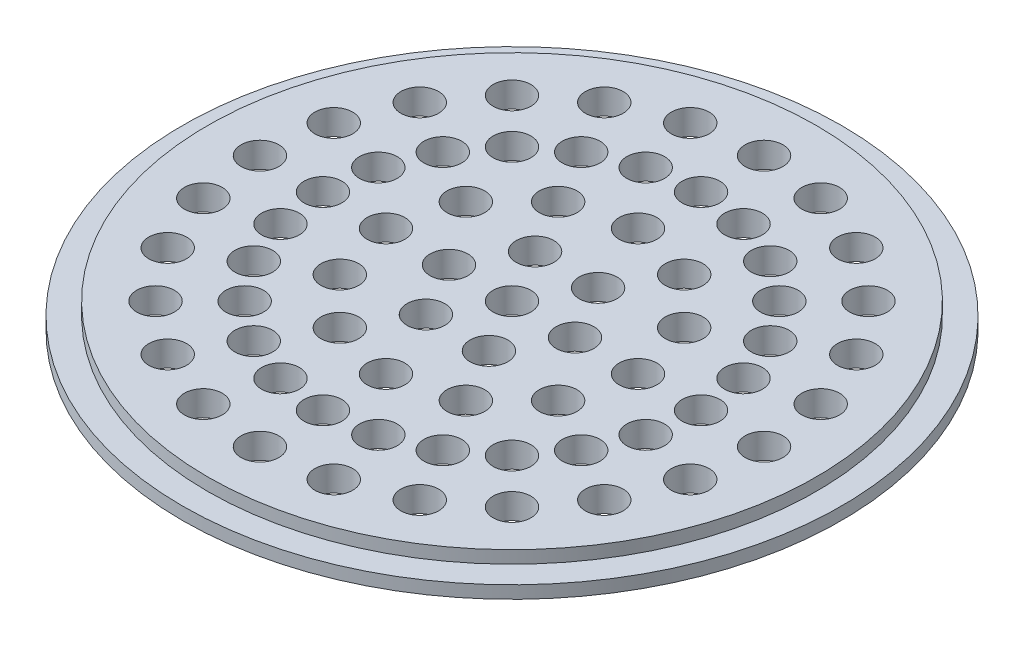
SolidWorks part; units mm, degrees
ref_plane "Спереди" through (0, 0, 0) normal (0, 0, 1) x (1, 0, 0)
ref_plane "Сверху" through (0, 0, 0) normal (0, 1, 0) x (1, 0, 0)
ref_plane "Справа" through (0, 0, 0) normal (1, 0, 0) x (0, 0, -1)
sketch "Эскиз1" plane through (0, 0, 0) normal (0, 1, 0) x (1, 0, 0)
  circle A0 centre (0, 0) radius 26.15
  dimension "D1" = 52.3
extrude "Бобышка-Вытянуть1" add sketch "Эскиз1" along normal blind 1
sketch "Эскиз2" plane through (0, 1, 0) normal (0, 1, 0) x (1, 0, 0)
  circle A0 centre (0, 0) radius 24.15
  dimension "D1" = 48.3
extrude "Бобышка-Вытянуть2" add sketch "Эскиз2" along normal blind 1
sketch "Эскиз3" plane through (0, 2, 0) normal (0, 1, 0) x (1, 0, 0)
  line L0 (0, 24.15) -> (0, -24.15) construction
  line L1 (0, 0) -> (5, 0) construction
  line L2 (0, 0) -> (2.5, -4.3301) construction
  line L3 (0, 0) -> (-2.5, -4.3301) construction
  line L4 (0, 0) -> (-5, 0) construction
  line L5 (0, 0) -> (-2.5, 4.3301) construction
  line L6 (0, 0) -> (2.5, 4.3301) construction
  circle A0 centre (0, 0) radius 1.5
  circle A1 centre (0, 0) radius 24.15 construction
  circle A2 centre (0, 0) radius 24.15 construction
  circle A3 centre (5, 0) radius 1.5
  circle A4 centre (10, 0) radius 1.5
  circle A5 centre (15, 0) radius 1.5
  circle A6 centre (20, 0) radius 1.5
  circle A7 centre (2.5, -4.3301) radius 1.5
  circle A8 centre (5, -8.6603) radius 1.5
  circle A9 centre (7.5, -12.9904) radius 1.5
  circle A10 centre (10, -17.3205) radius 1.5
  circle A11 centre (-2.5, -4.3301) radius 1.5
  circle A12 centre (-5, -8.6603) radius 1.5
  circle A13 centre (-7.5, -12.9904) radius 1.5
  circle A14 centre (-10, -17.3205) radius 1.5
  circle A15 centre (-5, 0) radius 1.5
  circle A16 centre (-10, 0) radius 1.5
  circle A17 centre (-15, 0) radius 1.5
  circle A18 centre (-20, 0) radius 1.5
  circle A19 centre (-2.5, 4.3301) radius 1.5
  circle A20 centre (-5, 8.6603) radius 1.5
  circle A21 centre (-7.5, 12.9904) radius 1.5
  circle A22 centre (-10, 17.3205) radius 1.5
  circle A23 centre (2.5, 4.3301) radius 1.5
  circle A24 centre (5, 8.6603) radius 1.5
  circle A25 centre (7.5, 12.9904) radius 1.5
  circle A26 centre (10, 17.3205) radius 1.5
  circle A27 centre (8.6603, -5) radius 1.5
  circle A28 centre (12.9904, -7.5) radius 1.5
  circle A29 centre (17.3205, -10) radius 1.5
  circle A30 centre (5, -8.6603) radius 1.5
  circle A31 centre (7.5, -12.9904) radius 1.5
  circle A32 centre (10, -17.3205) radius 1.5
  circle A33 centre (0, -10) radius 1.5
  circle A34 centre (0, -15) radius 1.5
  circle A35 centre (0, -20) radius 1.5
  circle A36 centre (-5, -8.6603) radius 1.5
  circle A37 centre (-7.5, -12.9904) radius 1.5
  circle A38 centre (-10, -17.3205) radius 1.5
  circle A39 centre (-8.6603, -5) radius 1.5
  circle A40 centre (-12.9904, -7.5) radius 1.5
  circle A41 centre (-17.3205, -10) radius 1.5
  circle A42 centre (-10, 0) radius 1.5
  circle A43 centre (-15, 0) radius 1.5
  circle A44 centre (-20, 0) radius 1.5
  circle A45 centre (-8.6603, 5) radius 1.5
  circle A46 centre (-12.9904, 7.5) radius 1.5
  circle A47 centre (-17.3205, 10) radius 1.5
  circle A48 centre (-5, 8.6603) radius 1.5
  circle A49 centre (-7.5, 12.9904) radius 1.5
  circle A50 centre (-10, 17.3205) radius 1.5
  circle A51 centre (0, 10) radius 1.5
  circle A52 centre (0, 15) radius 1.5
  circle A53 centre (0, 20) radius 1.5
  circle A54 centre (5, 8.6603) radius 1.5
  circle A55 centre (7.5, 12.9904) radius 1.5
  circle A56 centre (10, 17.3205) radius 1.5
  circle A57 centre (8.6603, 5) radius 1.5
  circle A58 centre (12.9904, 7.5) radius 1.5
  circle A59 centre (17.3205, 10) radius 1.5
  circle A60 centre (14.4889, -3.8823) radius 1.5
  circle A61 centre (19.3185, -5.1764) radius 1.5
  circle A62 centre (12.9904, -7.5) radius 1.5
  circle A63 centre (17.3205, -10) radius 1.5
  circle A64 centre (10.6066, -10.6066) radius 1.5
  circle A65 centre (14.1421, -14.1421) radius 1.5
  circle A66 centre (7.5, -12.9904) radius 1.5
  circle A67 centre (10, -17.3205) radius 1.5
  circle A68 centre (3.8823, -14.4889) radius 1.5
  circle A69 centre (5.1764, -19.3185) radius 1.5
  circle A70 centre (0, -15) radius 1.5
  circle A71 centre (0, -20) radius 1.5
  circle A72 centre (-3.8823, -14.4889) radius 1.5
  circle A73 centre (-5.1764, -19.3185) radius 1.5
  circle A74 centre (-7.5, -12.9904) radius 1.5
  circle A75 centre (-10, -17.3205) radius 1.5
  circle A76 centre (-10.6066, -10.6066) radius 1.5
  circle A77 centre (-14.1421, -14.1421) radius 1.5
  circle A78 centre (-12.9904, -7.5) radius 1.5
  circle A79 centre (-17.3205, -10) radius 1.5
  circle A80 centre (-14.4889, -3.8823) radius 1.5
  circle A81 centre (-19.3185, -5.1764) radius 1.5
  circle A82 centre (-15, 0) radius 1.5
  circle A83 centre (-20, 0) radius 1.5
  circle A84 centre (-14.4889, 3.8823) radius 1.5
  circle A85 centre (-19.3185, 5.1764) radius 1.5
  circle A86 centre (-12.9904, 7.5) radius 1.5
  circle A87 centre (-17.3205, 10) radius 1.5
  circle A88 centre (-10.6066, 10.6066) radius 1.5
  circle A89 centre (-14.1421, 14.1421) radius 1.5
  circle A90 centre (-7.5, 12.9904) radius 1.5
  circle A91 centre (-10, 17.3205) radius 1.5
  circle A92 centre (-3.8823, 14.4889) radius 1.5
  circle A93 centre (-5.1764, 19.3185) radius 1.5
  circle A94 centre (0, 15) radius 1.5
  circle A95 centre (0, 20) radius 1.5
  circle A96 centre (3.8823, 14.4889) radius 1.5
  circle A97 centre (5.1764, 19.3185) radius 1.5
  circle A98 centre (7.5, 12.9904) radius 1.5
  circle A99 centre (10, 17.3205) radius 1.5
  circle A100 centre (10.6066, 10.6066) radius 1.5
  circle A101 centre (14.1421, 14.1421) radius 1.5
  circle A102 centre (12.9904, 7.5) radius 1.5
  circle A103 centre (17.3205, 10) radius 1.5
  circle A104 centre (14.4889, 3.8823) radius 1.5
  circle A105 centre (19.3185, 5.1764) radius 1.5
  point P68 (0, 0)
  point P134 (0, 0)
  point P228 (0, 0)
  dimension "D1" = 3
  dimension "D3" = 5
  dimension "D2" = 5
  dimension "D4" = 6
  dimension "D5" = 12
  dimension "D6" = 24
extrude "Вырез-Вытянуть1" cut sketch "Эскиз3" against normal through all
